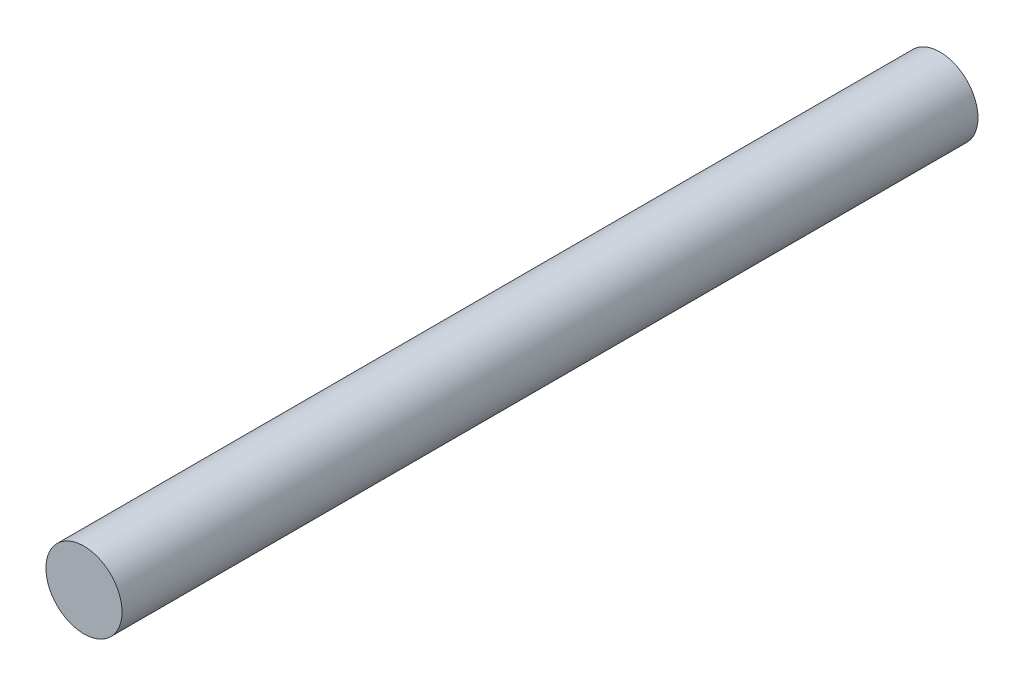
SolidWorks part; units mm, degrees
ref_plane "Front Plane" through (0, 0, 0) normal (0, 0, 1) x (1, 0, 0)
ref_plane "Top Plane" through (0, 0, 0) normal (0, 1, 0) x (1, 0, 0)
ref_plane "Right Plane" through (0, 0, 0) normal (1, 0, 0) x (0, 0, -1)
sketch "Sketch1" plane through (0, 0, 0) normal (0, 0, 1) x (1, 0, 0)
  circle A0 centre (0, 0) radius 2
extrude "Boss-Extrude1" add sketch "Sketch1" along normal blind 45
